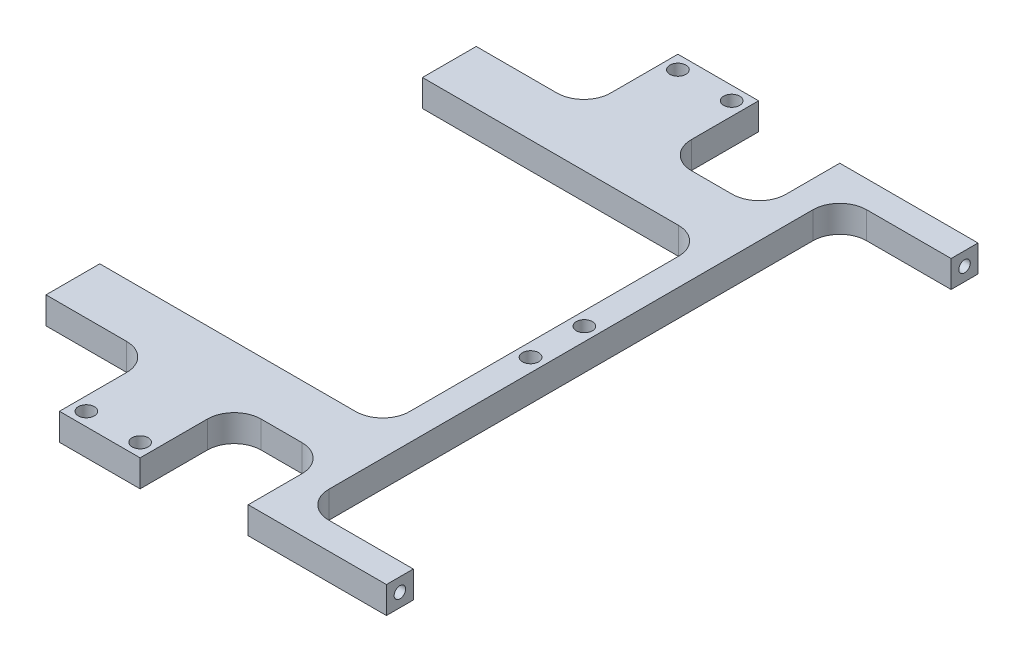
SolidWorks part; units mm, degrees
material "6061 Alloy"
ref_plane "Front Plane" through (0, 0, 0) normal (0, 0, 1) x (1, 0, 0)
ref_plane "Top Plane" through (0, 0, 0) normal (0, 1, 0) x (1, 0, 0)
ref_plane "Right Plane" through (0, 0, 0) normal (1, 0, 0) x (0, 0, -1)
sketch "Sketch1" plane through (0, 0, 0) normal (0, 1, 0) x (1, 0, 0)
  line L0 (-49.7205, 0) -> (49.7205, 0) construction
  line L1 (-49.7205, 69.85) -> (49.7205, 69.85)
  line L2 (-49.7205, 69.85) -> (-49.7205, -69.85)
  line L3 (-49.7205, -69.85) -> (49.7205, -69.85)
  line L4 (49.7205, 69.85) -> (49.7205, -69.85)
  line L6 (0, 69.85) -> (0, -69.85) construction
  dimension "D1" = 99.441
  dimension "D2" = 139.7
extrude "Extrude1" add sketch "Sketch1" along normal blind 6.35
sketch "Sketch2" plane through (0, 6.35, 0) normal (0, 1, 0) x (-1, 0, 0)
  line L0 (-49.7205, 69.85) -> (-49.7205, -69.85) construction
  line L1 (49.7205, -69.85) -> (-17.0815, -69.85)
  line L2 (49.7205, -69.85) -> (49.7205, -50.8)
  line L3 (49.7205, -50.8) -> (-17.0815, -50.8)
  line L4 (-17.0815, -69.85) -> (-17.0815, -50.8)
  line L5 (49.7205, 69.85) -> (-17.0815, 69.85)
  line L6 (49.7205, 69.85) -> (49.7205, 50.8)
  line L7 (49.7205, 50.8) -> (-17.0815, 50.8)
  line L8 (-17.0815, 69.85) -> (-17.0815, 50.8)
  line L9 (-49.7205, -63.5) -> (-23.4315, -63.5)
  line L10 (-49.7205, -63.5) -> (-49.7205, 63.5)
  line L11 (-49.7205, 63.5) -> (-23.4315, 63.5)
  line L12 (-23.4315, -63.5) -> (-23.4315, 63.5)
  line L13 (-49.7205, -69.85) -> (49.7205, -69.85) construction
  line L14 (49.7205, 69.85) -> (-49.7205, 69.85) construction
  line L15 (49.7205, -69.85) -> (49.7205, 69.85) construction
  line L16 (49.7205, -38.1) -> (-17.0815, -38.1)
  line L17 (49.7205, -38.1) -> (49.7205, 38.1)
  line L18 (49.7205, 38.1) -> (-17.0815, 38.1)
  line L19 (-17.0815, -38.1) -> (-17.0815, 38.1)
  dimension "D1" = 101.6
  dimension "D2" = 66.802
  dimension "D3" = 6.35
  dimension "D4" = 6.35
  dimension "D5" = 6.35
  dimension "D6" = 12.7
  dimension "D7" = 12.7
extrude "Cut-Extrude1" cut sketch "Sketch2" against normal blind 6.35
fillet "Fillet1" radius 6.35 6 edges at (23.4315, 3.175, 63.5) (23.4315, 3.175, -63.5) (17.0815, 3.175, -50.8) (17.0815, 3.175, 50.8) (17.0815, 3.175, 38.1) (17.0815, 3.175, -38.1)
hole_wizard "Tap Drill for #6 Tap1" positions "3DSketch1" profile "Sketch3" hole size "#6-32" standard "Ansi Inch"
sketch3d "3DSketch1"
  line L0 (-49.7205, 6.35, -50.8) -> (-49.7205, 6.35, -38.1) construction
  line L1 (-49.7205, 6.35, 38.1) -> (-49.7205, 6.35, 50.8) construction
  line L2 (-49.7205, 0, 50.8) -> (-49.7205, 6.35, 50.8) construction
  line L3 (-49.7205, 0, -38.1) -> (-49.7205, 6.35, -38.1) construction
  point P0 (-49.7205, 3.175, -44.45)
  point P2 (-49.7205, 3.175, 44.45)
  dimension "D1" = 3.175
  dimension "D2" = 3.175
  dimension "D3" = 6.35
  dimension "D4" = 6.35
sketch "Sketch3" plane through (-49.7205, 3.175, -44.45) normal (0, 1, 0) x (0, 0, 1)
  line L0 (0, 0) -> (0, 13.5127)
  line L1 (0, 13.5127) -> (1.3525, 12.7)
  line L2 (1.3525, 12.7) -> (1.3525, 0)
  line L5 (1.3525, 0) -> (0, 0)
  line L10 (0, 13.5127) -> (-1.3526, 12.7) construction
  line L11 (0, -6.35) -> (0, 107.95) construction
  dimension "Hole Dia." = 2.7051
  dimension "Hole Depth" = 12.7
  dimension "Drill Angle" = 118
hole_wizard "Tap Drill for #6 Tap2" positions "3DSketch2" profile "Sketch4" hole size "#6-32" standard "Ansi Inch"
sketch3d "3DSketch2"
  line L0 (49.7205, 6.35, -66.675) -> (49.7205, 0, -66.675) construction
  line L1 (49.7205, 6.35, -63.5) -> (49.7205, 6.35, -69.85) construction
  line L2 (49.7205, 0, -63.5) -> (49.7205, 0, -69.85) construction
  line L4 (49.7205, 6.35, -69.85) -> (49.7205, 0, -69.85) construction
  line L5 (49.7205, 3.175, -69.85) -> (49.7205, 3.175, -63.5) construction
  line L6 (49.7205, 0, -63.5) -> (49.7205, 6.35, -63.5) construction
  line L8 (49.7205, 6.35, 66.675) -> (49.7205, 0, 66.675) construction
  line L9 (49.7205, 6.35, 69.85) -> (49.7205, 6.35, 63.5) construction
  line L10 (49.7205, 0, 69.85) -> (49.7205, 0, 63.5) construction
  line L12 (49.7205, 0, 63.5) -> (49.7205, 6.35, 63.5) construction
  line L13 (49.7205, 3.175, 63.5) -> (49.7205, 3.175, 69.85) construction
  line L14 (49.7205, 6.35, 69.85) -> (49.7205, 0, 69.85) construction
  point P0 (49.7205, 3.175, -66.675)
  point P2 (49.7205, 3.175, 66.675)
sketch "Sketch4" plane through (49.7205, 3.175, -66.675) normal (0, 1, 0) x (0, 0, -1)
  line L0 (0, 0) -> (0, 13.5127)
  line L1 (0, 13.5127) -> (1.3525, 12.7)
  line L2 (1.3525, 12.7) -> (1.3525, 0)
  line L5 (1.3525, 0) -> (0, 0)
  line L10 (0, 13.5127) -> (-1.3525, 12.7) construction
  line L11 (0, -6.35) -> (0, 107.95) construction
  dimension "Hole Dia." = 2.7051
  dimension "Hole Depth" = 12.7
  dimension "Drill Angle" = 118
hole_wizard "#6 Clearance Hole1" positions "3DSketch3" profile "Sketch5" hole size "#6" standard "Ansi Inch"
sketch3d "3DSketch3"
  line L0 (23.4315, 0, -57.15) -> (23.4315, 0, 57.15) construction
  line L1 (49.7205, 0, -69.85) -> (17.0815, 0, -69.85) construction
  point P0 (20.2565, 0, 6.35)
  point P2 (20.2565, 0, -6.35)
  dimension "D1" = 3.175
  dimension "D2" = 12.7
  dimension "D3" = 63.5
sketch "Sketch5" plane through (20.2565, 0, 6.35) normal (1, 0, 0) x (0, 0, -1)
  line L0 (0, 0) -> (0, 13.8408)
  line L1 (0, 13.8408) -> (1.8986, 12.7)
  line L2 (1.8986, 12.7) -> (1.8986, 0)
  line L5 (1.8986, 0) -> (0, 0)
  line L10 (0, 13.8408) -> (-1.8986, 12.7) construction
  line L11 (0, -6.35) -> (0, 107.95) construction
  dimension "Hole Dia." = 3.7973
  dimension "Hole Depth" = 12.7
  dimension "Drill Angle" = 118
sketch "Sketch6" plane through (0, 0, 0) normal (0, -1, 0) x (1, 0, 0)
  line L0 (10.7315, 50.8) -> (-49.7205, 50.8) construction
  line L1 (-5.2705, 50.8) -> (-24.3205, 50.8)
  line L2 (-5.2705, 50.8) -> (-5.2705, 73.025)
  line L3 (-5.2705, 73.025) -> (-24.3205, 73.025)
  line L4 (-24.3205, 50.8) -> (-24.3205, 73.025)
  line L5 (-49.7205, -50.8) -> (10.7315, -50.8) construction
  line L6 (-5.2705, -50.8) -> (-24.3205, -50.8)
  line L7 (-5.2705, -50.8) -> (-5.2705, -73.025)
  line L8 (-5.2705, -73.025) -> (-24.3205, -73.025)
  line L9 (-24.3205, -50.8) -> (-24.3205, -73.025)
  line L12 (-49.7205, 38.1) -> (-49.7205, 50.8) construction
  dimension "D1" = 19.05
  dimension "D2" = 25.4
  dimension "D3" = 22.225
  dimension "D4" = 22.225
extrude "Extrude2" add sketch "Sketch6" against normal blind 6.35
fillet "Fillet2" radius 6.35 4 edges at (-5.2705, 3.175, -50.8) (-24.3205, 3.175, -50.8) (-24.3205, 3.175, 50.8) (-5.2705, 3.175, 50.8)
hole_wizard "#6 Clearance Hole2" positions "3DSketch4" profile "Sketch7" hole size "#6" standard "Ansi Inch"
sketch3d "3DSketch4"
  line L0 (-5.2705, 0, 73.025) -> (-24.3205, 0, 73.025) construction
  line L1 (-5.2705, 0, 57.15) -> (-5.2705, 0, 73.025) construction
  line L2 (-5.2705, 0, -73.025) -> (-5.2705, 0, -57.15) construction
  line L3 (-24.3205, 0, -73.025) -> (-5.2705, 0, -73.025) construction
  point P0 (-8.4455, 0, 69.85)
  point P2 (-21.1455, 0, -69.85)
  point P4 (-21.1455, 0, 69.85)
  point P6 (-8.4455, 0, -69.85)
  dimension "D1" = 3.175
  dimension "D2" = 12.7
  dimension "D3" = 3.175
  dimension "D4" = 3.175
  dimension "D5" = 3.175
  dimension "D6" = 12.7
sketch "Sketch7" plane through (-8.4455, 0, 69.85) normal (1, 0, 0) x (0, 0, -1)
  line L0 (0, 0) -> (0, 13.8408)
  line L1 (0, 13.8408) -> (1.8986, 12.7)
  line L2 (1.8986, 12.7) -> (1.8986, 0)
  line L5 (1.8986, 0) -> (0, 0)
  line L10 (0, 13.8408) -> (-1.8987, 12.7) construction
  line L11 (0, -6.35) -> (0, 107.95) construction
  dimension "Hole Dia." = 3.7973
  dimension "Hole Depth" = 12.7
  dimension "Drill Angle" = 118
